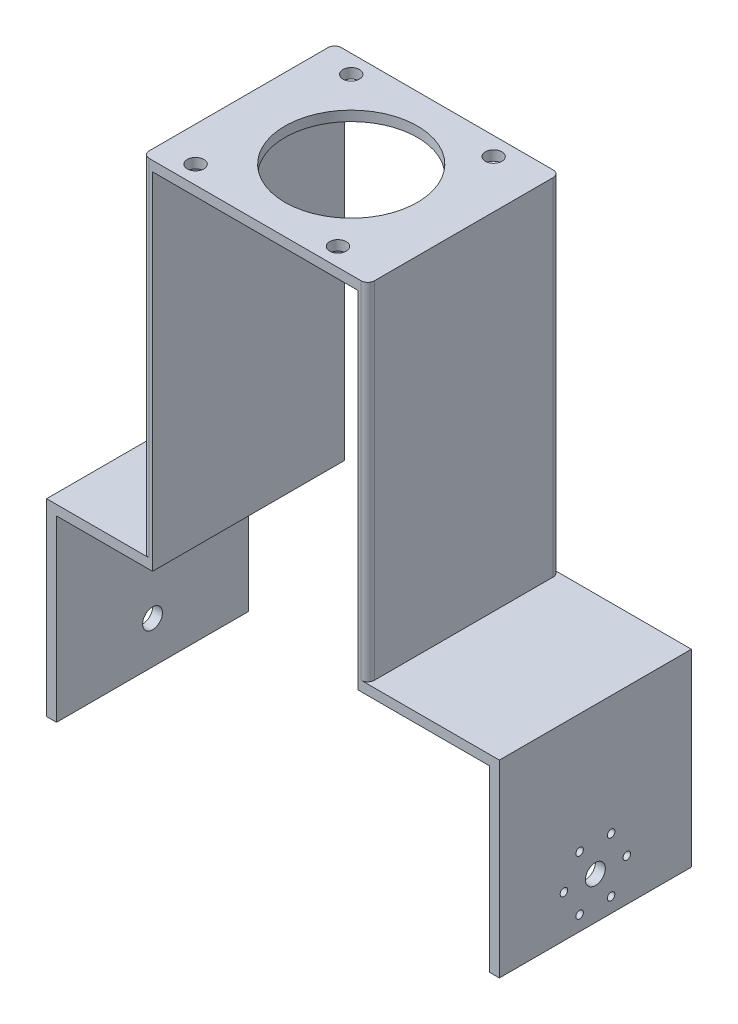
SolidWorks part; units mm, degrees
material "1060 Alloy"
ref_plane "Front Plane" through (0, 0, 0) normal (0, 0, 1) x (1, 0, 0)
ref_plane "Top Plane" through (0, 0, 0) normal (0, 1, 0) x (1, 0, 0)
ref_plane "Right Plane" through (0, 0, 0) normal (1, 0, 0) x (0, 0, -1)
sketch "Sketch2" plane through (0, 0, 0) normal (0, 0, 1) x (1, 0, 0)
  line L0 (2, 51.8967) -> (36, 51.8967)
  line L1 (36, 51.8967) -> (36, -52.6033)
  line L2 (36, -52.6033) -> (75.75, -52.6033)
  line L3 (75.75, -52.6033) -> (75.75, -109.6033)
  line L4 (2, 51.8967) -> (-32, 51.8967)
  line L5 (-32, 51.8967) -> (-32, -52.6033)
  line L6 (-32, -52.6033) -> (-61, -52.6033)
  line L7 (-61, -52.6033) -> (-61, -109.6033)
  line L8 (-58, -55.6033) -> (-58, -109.6033)
  line L9 (-29, -55.6033) -> (-58, -55.6033)
  line L10 (-29, 48.8967) -> (-29, -55.6033)
  line L11 (2, 48.8967) -> (-29, 48.8967)
  line L12 (2, 48.8967) -> (33, 48.8967)
  line L13 (33, 48.8967) -> (33, -55.6033)
  line L14 (33, -55.6033) -> (72.75, -55.6033)
  line L15 (72.75, -55.6033) -> (72.75, -109.6033)
  line L16 (-61, -109.6033) -> (-58, -109.6033)
  line L17 (72.75, -109.6033) -> (75.75, -109.6033)
  dimension "D1" = 34
  dimension "D2" = 104.5
  dimension "D3" = 39.75
  dimension "D4" = 57
  dimension "D5" = 34
  dimension "D6" = 29
  dimension "D7" = 3
extrude "Boss-Extrude1" add sketch "Sketch2" along normal blind 58
sketch "Sketch3" plane through (0, 51.8967, 0) normal (0, 1, 0) x (1, 0, 0)
  line L0 (-32, 0) -> (-21.5, 0) construction
  line L1 (36, 0) -> (-32, 0) construction
  line L2 (-21.5, 0) -> (-21.5, -5.5) construction
  line L3 (-32, -29) -> (36, -29) construction
  line L4 (-32, -58) -> (-32, 0) construction
  line L5 (36, -58) -> (36, 0) construction
  line L6 (0, 0) -> (0, -57.402) construction
  circle A0 centre (-21.5, -5.5) radius 2.5
  circle A1 centre (21.5, -5.5) radius 2.5
  circle A2 centre (21.5, -52.5) radius 2.5
  circle A3 centre (-21.5, -52.5) radius 2.5
  circle A4 centre (2, -29) radius 20
  dimension "D3" = 5
  dimension "D4" = 40
  dimension "D1" = 10.5
  dimension "D2" = 5.5
  dimension "D5" = 43
extrude "Cut-Extrude1" cut sketch "Sketch3" against normal blind 58
sketch "Sketch5" plane through (-61, 0, 0) normal (-1, 0, 0) x (0, 0, 1)
  line L0 (0, -109.6033) -> (0, -96.9033) construction
  line L1 (0, -52.6033) -> (0, -109.6033) construction
  line L2 (0, -96.9033) -> (29, -96.9033) construction
  circle A0 centre (29, -96.9033) radius 3
  dimension "D2" = 6
  dimension "D1" = 12.7
extrude "Cut-Extrude3" cut sketch "Sketch5" against normal blind 58
sketch "Sketch7" plane through (75.75, 0, 0) normal (1, 0, 0) x (0, 0, -1)
  line L0 (-29, -109.6033) -> (-29, -96.9024) construction
  line L1 (-58, -109.6033) -> (0, -109.6033) construction
sketch "Sketch8" plane through (75.75, -106.8485, 47.0728) normal (1, 0, 0) x (0, 0, -1)
  line L0 (18.0728, 9.946) -> (27.5728, 9.946) construction
  circle A0 centre (18.0728, 9.946) radius 9.5
  dimension "D1" = 19
hole_wizard "#4-40 Tapped Hole2" positions "Sketch14" profile "Sketch13" tap size "#4-40" standard "ANSI Inch"
sketch "Sketch14" plane through (75.75, 0, 0) normal (1, 0, 0) x (0, 0, -1)
  point P0 (-19.5, -96.9024)
  point P8 (-24.25, -105.1297)
  point P9 (-33.75, -105.1297)
  point P10 (-38.5, -96.9024)
  point P11 (-33.75, -88.6752)
  point P12 (-24.25, -88.6752)
  dimension "D1" = 6
sketch "Sketch13" plane through (75.75, -96.9024, 19.5) normal (0, 1, 0) x (0, 0, -1)
  line L0 (0, 0) -> (0, 8.2792)
  line L1 (0, 8.2792) -> (1.1303, 7.6)
  line L2 (1.1303, 7.6) -> (1.1303, 0)
  line L5 (1.1303, 0) -> (0, 0)
  line L10 (0, 8.2792) -> (-1.1303, 7.6) construction
  line L11 (0, -6.35) -> (0, 107.95) construction
  dimension "Tap Drill Dia." = 2.2606
  dimension "Tap Drill Depth" = 7.6
  dimension "Drill Angle" = 118
cosmetic thread "Hole Thread7"
cosmetic thread "Hole Thread8"
cosmetic thread "Hole Thread9"
cosmetic thread "Hole Thread10"
cosmetic thread "Hole Thread11"
cosmetic thread "Hole Thread12"
sketch "Sketch15" plane through (75.75, 0, 0) normal (1, 0, 0) x (0, 0, -1)
  circle A0 centre (-29, -96.9024) radius 3
  dimension "D1" = 6
extrude "Cut-Extrude4" cut sketch "Sketch15" against normal blind 10
fillet "Fillet1" radius 2 1 edges at (36, -0.3533, 58)
fillet "Fillet2" radius 2 1 edges at (36, -0.3533, 0)
fillet "Fillet3" radius 2 1 edges at (-32, -0.3533, 0)
fillet "Fillet4" radius 2 1 edges at (-32, -0.3533, 58)
